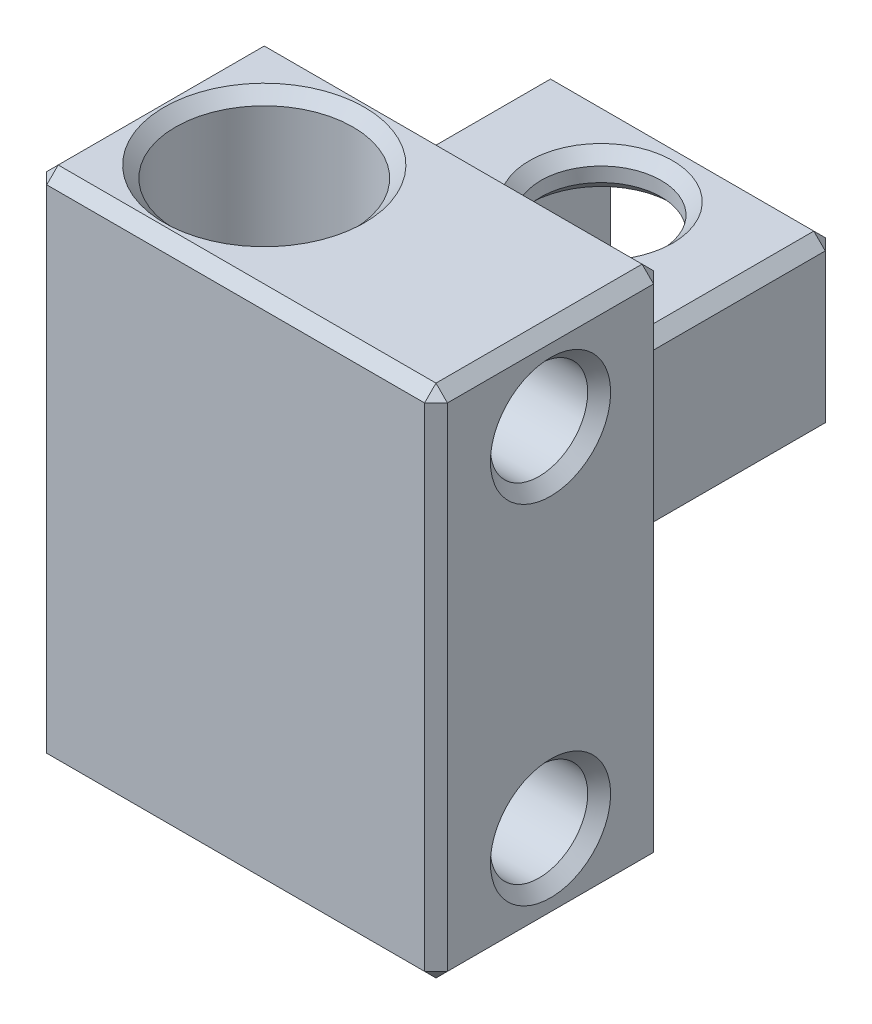
SolidWorks part; units mm, degrees
material "ABS"
ref_plane "Front Plane" through (0, 0, 0) normal (0, 0, 1) x (1, 0, 0)
ref_plane "Top Plane" through (0, 0, 0) normal (0, 1, 0) x (1, 0, 0)
ref_plane "Right Plane" through (0, 0, 0) normal (1, 0, 0) x (0, 0, -1)
sketch "Sketch1" plane through (0, 0, 0) normal (0, 1, 0) x (1, 0, 0)
  line L1 (0, 0) -> (35, 0)
  line L2 (0, 0) -> (0, 20)
  line L3 (0, 20) -> (35, 20)
  line L4 (35, 0) -> (35, 20)
  dimension "D1" = 20
  dimension "D2" = 35
extrude "Boss-Extrude1" add sketch "Sketch1" along normal blind 45
sketch "Sketch2" plane through (0, 45, 0) normal (0, 1, 0) x (1, 0, 0)
  line L0 (0, 0) -> (20, 20) construction
  line L1 (35, 20) -> (0, 20) construction
  circle A0 centre (10, 10) radius 7.75
extrude "Cut-Extrude1" cut sketch "Sketch2" against normal through all
sketch "Sketch3" plane through (35, 0, 0) normal (1, 0, 0) x (0, 0, -1)
  line L0 (0, 45) -> (20, 45) construction
  line L1 (0, 0) -> (20, 0) construction
  circle A1 centre (10, 37.6875) radius 4.25
  circle A2 centre (10, 7.3125) radius 4.25
  dimension "D1" = 7.3125
  dimension "D2" = 7.3125
extrude "Cut-Extrude2" cut sketch "Sketch3" against normal blind 10
sketch "Sketch4" plane through (0, 0, -20) normal (0, 0, -1) x (-1, 0, 0)
  line L0 (0, 45) -> (0, 0) construction
  line L1 (0, 15) -> (-25, 15)
  line L2 (0, 15) -> (0, 30)
  line L3 (0, 30) -> (-25, 30)
  line L4 (-25, 15) -> (-25, 30)
  point P6 (0, 22.5)
  point P7 (0, 22.5)
  dimension "D1" = 15
  dimension "D2" = 25
extrude "Boss-Extrude2" add sketch "Sketch4" along normal blind 25
sketch "Sketch5" plane through (0, 30, 0) normal (0, 1, 0) x (1, 0, 0)
  line L0 (0, 45) -> (25, 45) construction
  line L1 (19.75, 45) -> (5.25, 45)
  line L2 (19.75, 45) -> (19.75, 28.75)
  line L3 (19.75, 28.75) -> (5.25, 28.75)
  line L4 (5.25, 45) -> (5.25, 28.75)
  line L6 (19.75, 45) -> (25, 45) construction
  line L7 (5.25, 45) -> (0, 45) construction
  dimension "D1" = 14.5
  dimension "D2" = 16.25
extrude "Cut-Extrude3" cut sketch "Sketch5" against normal through all
sketch "Sketch6" plane through (5.25, 0, 0) normal (1, 0, 0) x (0, 0, -1)
  line L0 (28.75, 15) -> (28.75, 30) construction
  line L1 (45, 30) -> (28.75, 30)
  line L2 (45, 30) -> (45, 26.75)
  line L3 (45, 26.75) -> (28.75, 26.75)
  line L4 (28.75, 30) -> (28.75, 26.75)
  line L6 (45, 15) -> (28.75, 15)
  line L7 (45, 15) -> (45, 18.25)
  line L8 (45, 18.25) -> (28.75, 18.25)
  line L9 (28.75, 15) -> (28.75, 18.25)
  dimension "D1" = 3.25
extrude "Boss-Extrude3" add sketch "Sketch6" along normal up to next
sketch "Sketch7" plane through (0, 18.25, 0) normal (0, 1, 0) x (1, 0, 0)
  circle A0 centre (12.5, 36.9171) radius 5.25
extrude "Cut-Extrude4" cut sketch "Sketch7" against normal through all both and the other way through all
chamfer "Chamfer1" distance 1 angle 45 30 edges at (17.75, 30, -36.9171) (10, 0, -2.25) (10, 45, -2.25) (12.5, 26.75, -31.6671) (12.5, 18.25, -42.1671) (7.25, 15, -36.9171) (12.5, 15, -20) (35, 22.5, -20) (12.5, 30, -20) (12.5, 30, -45) (25, 30, -32.5) (25, 22.5, -20) (25, 22.5, -45) (25, 15, -32.5) (35, 0, -10) (17.5, 0, -20) (0, 7.5, -20) (0, 15, -32.5) (0, 0, -10) (0, 22.5, 0) (17.5, 0, 0) (35, 22.5, 0) (17.5, 45, -20) (35, 45, -10) (17.5, 45, 0) (0, 45, -10) (0, 37.5, -20) (0, 30, -32.5) (0, 22.5, -45) (12.5, 15, -45)
chamfer "Chamfer2" distance 1 angle 45 2 edges at (35, 7.3125, -14.25) (35, 37.6875, -14.25)
